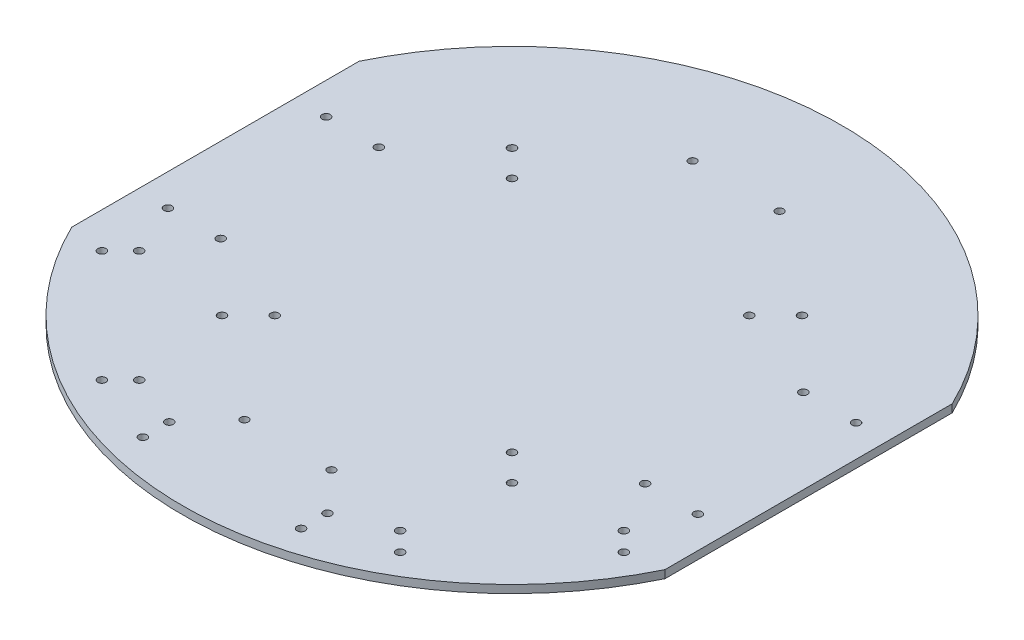
SolidWorks part; units mm, degrees
material "Pine"
ref_plane "Front Plane" through (0, 0, 0) normal (0, 0, 1) x (1, 0, 0)
ref_plane "Top Plane" through (0, 0, 0) normal (0, 1, 0) x (1, 0, 0)
ref_plane "Right Plane" through (0, 0, 0) normal (1, 0, 0) x (0, 0, -1)
sketch "Sketch1" plane through (0, 0, 0) normal (0, 1, 0) x (1, 0, 0)
  line L0 (-112.5, 54.4862) -> (-112.5, -54.4862)
  line L1 (-45, 45) -> (45, 45) construction
  line L2 (-45, 45) -> (-45, -45) construction
  line L3 (-45, -45) -> (45, -45) construction
  line L4 (45, 45) -> (45, -45) construction
  line L5 (0, -45) -> (0, 45) construction
  line L6 (-45, 0) -> (45, 0) construction
  line L7 (-55, 55) -> (55, 55) construction
  line L8 (-55, 55) -> (-55, -55) construction
  line L9 (-55, -55) -> (55, -55) construction
  line L10 (55, 55) -> (55, -55) construction
  line L11 (0, -55) -> (0, 55) construction
  line L12 (-55, 0) -> (55, 0) construction
  line L13 (112.5, 54.4862) -> (112.5, -54.4862)
  circle A0 centre (0, 0) radius 125
  circle A1 centre (-55, 55) radius 1.55
  circle A2 centre (55, 55) radius 1.55
  circle A3 centre (55, -55) radius 1.55
  circle A4 centre (-55, -55) radius 1.55
  circle A5 centre (-45, 45) radius 1.55
  circle A6 centre (45, 45) radius 1.55
  circle A7 centre (45, -45) radius 1.55
  circle A8 centre (-45, -45) radius 1.55
  point P14 (62.5, -59.053)
  point P22 (49.1007, -47.5)
  point P23 (66.0331, 62.5)
  dimension "D5" = 250
  dimension "D7" = 3.1
  dimension "D10" = 3.1
  dimension "D1" = 90
  dimension "D2" = 90
  dimension "D3" = 110
  dimension "D4" = 110
  dimension "D6" = 112.5
  dimension "D8" = 2
  dimension "D9" = 2
  dimension "D11" = 2
  dimension "D12" = 2
extrude "Boss-Extrude1" add sketch "Sketch1" along normal blind 3 contours L13 A0 L0 A8 A7 A6 A5 A4 A3 A2 A1
sketch "Sketch2" plane through (0, 3, 0) normal (0, 1, 0) x (1, 0, 0)
  line L0 (0, 0) -> (-112.5, 0) construction
  line L1 (-112.5, 54.4862) -> (-112.5, -54.4862) construction
  line L2 (0, 0) -> (0, 125) construction
  line L3 (-16.5, 85) -> (16.5, 85) construction
  arc A0 (112.5, 54.4862) -> (-112.5, 54.4862) centre (0, 0) ccw construction
  circle A1 centre (-16.5, 85) radius 1.5
  circle A2 centre (16.5, 85) radius 1.5
  circle A3 centre (16.5, -85) radius 1.5
  circle A4 centre (-16.5, -85) radius 1.5
  circle A5 centre (0, 85) radius 14 construction
  circle A6 centre (0, -85) radius 14 construction
  point P11 (0, 85)
  dimension "D2" = 3
  dimension "D4" = 28
  dimension "D1" = 33
  dimension "D3" = 40
extrude "Cut-Extrude1" cut sketch "Sketch2" against normal through all
sketch "Sketch3" plane through (0, 3, 0) normal (0, 1, 0) x (1, 0, 0)
  line L0 (-112.5, 0) -> (0, 0) construction
  line L1 (-112.5, 54.4862) -> (-112.5, -54.4862) construction
  line L2 (0, 0) -> (0, 125) construction
  line L4 (-110.5, -35) -> (-70.5, -35) construction
  line L5 (-110.5, -35) -> (-110.5, 35) construction
  line L6 (-110.5, 35) -> (-70.5, 35) construction
  line L7 (-70.5, -35) -> (-70.5, 35) construction
  line L8 (-90.5, 35) -> (-90.5, -35) construction
  line L9 (-110.5, 0) -> (-70.5, 0) construction
  arc A0 (112.5, 54.4862) -> (-112.5, 54.4862) centre (0, 0) ccw construction
  circle A1 centre (-100.5, -30) radius 1.55
  circle A2 centre (-80.5, -30) radius 1.55
  circle A3 centre (-80.5, 30) radius 1.55
  circle A4 centre (-100.5, 30) radius 1.55
  circle A5 centre (100.5, 30) radius 1.55
  circle A6 centre (80.5, 30) radius 1.55
  circle A7 centre (100.5, -30) radius 1.55
  circle A8 centre (80.5, -30) radius 1.55
  point P5 (-90.5, 0)
  point P15 (-96.5886, -27.0003)
  dimension "D3" = 3.1
  dimension "D6" = 2
  dimension "D1" = 70
  dimension "D2" = 40
  dimension "D4" = 5
  dimension "D5" = 10
extrude "Cut-Extrude2" cut sketch "Sketch3" against normal through all
sketch "Sketch4" plane through (0, 3, 0) normal (0, 1, 0) x (1, 0, 0)
  line L0 (0, 0) -> (0, -125) construction
  line L2 (35, -95) -> (-35, -95) construction
  line L3 (35, -95) -> (35, -115) construction
  line L4 (35, -115) -> (-35, -115) construction
  line L5 (-35, -95) -> (-35, -115) construction
  line L6 (0, -115) -> (0, -95) construction
  line L7 (35, -105) -> (-35, -105) construction
  arc A0 (-112.5, -54.4862) -> (112.5, -54.4862) centre (0, 0) ccw construction
  circle A1 centre (-30, -110) radius 1.55
  circle A2 centre (-30, -100) radius 1.55
  circle A3 centre (30, -110) radius 1.55
  circle A4 centre (30, -100) radius 1.55
  point P6 (0, -105)
  point P12 (0, -103.8737)
  point P19 (0, -100.2612)
  dimension "D3" = 3.1
  dimension "D1" = 70
  dimension "D2" = 20
  dimension "D4" = 5
  dimension "D5" = 5
  dimension "D6" = 20
extrude "Cut-Extrude3" cut sketch "Sketch4" against normal through all
pattern_circular "CirPattern1" count 2 every 45 about axis through (0, 0, 0) along (0, 1, 0) of "Cut-Extrude3"
pattern_circular "CirPattern2" count 2 every 45 about axis through (0, 0, 0) along (0, 1, 0) of "Cut-Extrude3"
equation "\"D10@Sketch1\"=\"D7@Sketch1\""
